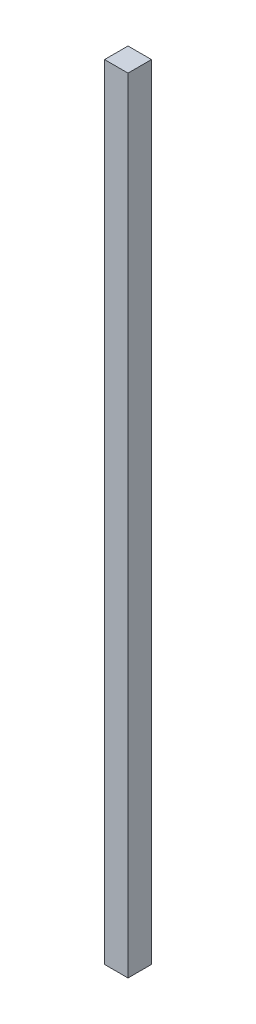
SolidWorks part; units mm, degrees
ref_plane "Спереди" through (0, 0, 0) normal (0, 0, 1) x (1, 0, 0)
ref_plane "Сверху" through (0, 0, 0) normal (0, 1, 0) x (1, 0, 0)
ref_plane "Справа" through (0, 0, 0) normal (1, 0, 0) x (0, 0, -1)
sketch "Эскиз1" plane through (0, 0, 0) normal (0, 1, 0) x (1, 0, 0)
  line L1 (5, 5) -> (-5, 5)
  line L2 (5, 5) -> (5, -5)
  line L3 (5, -5) -> (-5, -5)
  line L4 (-5, 5) -> (-5, -5)
  line L5 (5, 5) -> (-5, -5) construction
  line L6 (5, -5) -> (-5, 5) construction
  point P0 (0, 0)
  dimension "D1" = 10
extrude "Бобышка-Вытянуть1" add sketch "Эскиз1" along normal blind 334
